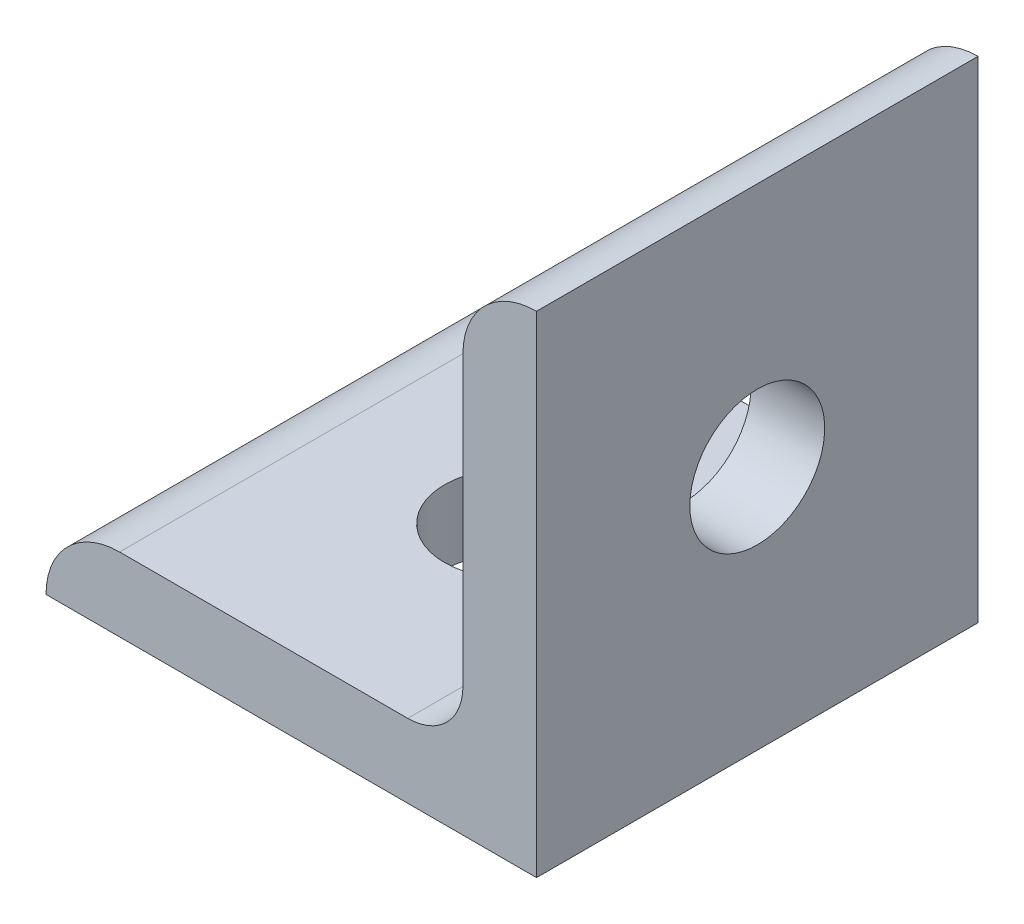
SolidWorks part; units mm, degrees
ref_plane "Front Plane" through (0, 0, 0) normal (0, 0, 1) x (1, 0, 0)
ref_plane "Top Plane" through (0, 0, 0) normal (0, 1, 0) x (1, 0, 0)
ref_plane "Right Plane" through (0, 0, 0) normal (1, 0, 0) x (0, 0, -1)
sketch "Sketch1" plane through (0, 0, 0) normal (0, 0, 1) x (1, 0, 0)
  line L0 (0, 0) -> (0, 20)
  line L1 (0, 0) -> (-20, 0)
  line L2 (-17, 3) -> (-5.25, 3)
  line L3 (-3, 5.25) -> (-3, 17)
  arc A0 (-20, 0) -> (-17, 3) centre (-17, 0) cw
  arc A1 (-3, 17) -> (0, 20) centre (0, 17) cw
  arc A2 (-5.25, 3) -> (-3, 5.25) centre (-5.25, 5.25) ccw
  point P11 (-11.125, 3)
  point P12 (-3, 11.125)
  dimension "D1" = 3
  dimension "D3" = 2.25
  dimension "D" = 3
  dimension "D2" = 3
  dimension "B" = 20
  dimension "C" = 20
extrude "Extrude1" add sketch "Sketch1" against normal mid plane 18
sketch "Sketch2" plane through (0, 3, 0) normal (0, 1, 0) x (1, 0, 0)
  circle A0 centre (-10, 0) radius 2.75
  dimension "hole" = 5.5
  dimension "hole height" = 10
extrude "Cut-Extrude1" cut sketch "Sketch2" against normal through all
sketch "Sketch3" plane through (-3, 0, 0) normal (-1, 0, 0) x (0, 0, 1)
  circle A0 centre (0, 10) radius 2.75
  dimension "D1" = 5.5
  dimension "D2" = 10
extrude "Cut-Extrude2" cut sketch "Sketch3" against normal through all
sketch "Sketch4" [suppressed] plane through (0, 6, 0) normal (0, 1, 0) x (1, 0, 0)
  line L0 (-84, 0) -> (-47.25, 0) construction
  line L1 (-47.25, 0) -> (-10.5, 0) construction
  circle A0 centre (-22.5, 0) radius 4.5
  circle A1 centre (-67.5, 0) radius 4.5
  dimension "D1" = 5.5
  dimension "D2" = 10
  dimension "D3" = 20
extrude "Cut-Extrude3" [suppressed] cut sketch "Sketch4" against normal through all
sketch "Sketch5" [suppressed] plane through (-6, 0, 0) normal (-1, 0, 0) x (0, 0, 1)
  circle A0 centre (0, 67.5) radius 4.5
  circle A1 centre (0, 22.5) radius 4.5
  dimension "D1" = 5.5
  dimension "D3" = 20
  dimension "D2" = 10
extrude "Cut-Extrude4" [suppressed] cut sketch "Sketch5" against normal through all
sketch "Sketch6" [suppressed] plane through (0, 3, 0) normal (0, 1, 0) x (1, 0, 0)
  line L0 (-10, 12.75) -> (-10, 19) construction
  line L1 (-5.25, -19) -> (-17, -19) construction
  line L2 (-10, -12.75) -> (-10, -19) construction
  line L3 (-5.25, 19) -> (-17, 19) construction
  circle A0 centre (-10, 10) radius 2.75
  circle A1 centre (-10, -10) radius 2.75
  dimension "D1" = 5.5
  dimension "D2" = 10
  dimension "distance" = 25.4
extrude "Cut-Extrude5" [suppressed] cut sketch "Sketch6" against normal through all
sketch "Sketch7" [suppressed] plane through (-3, 0, 0) normal (-1, 0, 0) x (0, 0, 1)
  line L0 (12.75, 10) -> (19, 10) construction
  line L2 (-12.75, 10) -> (-19, 10) construction
  line L4 (-19, 17) -> (-19, 5.25) construction
  line L5 (19, 17) -> (19, 5.25) construction
  circle A0 centre (-10, 10) radius 2.75
  circle A1 centre (10, 10) radius 2.75
  dimension "D2" = 5.5
  dimension "D1" = 25.4
  dimension "D3" = 10
extrude "Cut-Extrude6" [suppressed] cut sketch "Sketch7" against normal through all
sketch "Sketch8" [suppressed] plane through (0, 3, 0) normal (0, 1, 0) x (1, 0, 0)
  line L0 (-10, -10) -> (-10, -19) construction
  line L1 (-10, 10) -> (-10, 19) construction
  line L2 (-5.25, 19) -> (-37, 19) construction
  line L3 (-5.25, -19) -> (-37, -19) construction
  circle A0 centre (-30, -10) radius 2.75
  circle A1 centre (-10, -10) radius 2.75
  circle A2 centre (-10, 10) radius 2.75
  circle A3 centre (-30, 10) radius 2.75
  dimension "D1" = 5.5
  dimension "distance" = 25.4
  dimension "D2" = 10
  dimension "D3" = 20
extrude "Cut-Extrude7" [suppressed] cut sketch "Sketch8" against normal through all
sketch "Sketch9" [suppressed] plane through (-3, 0, 0) normal (-1, 0, 0) x (0, 0, 1)
  line L0 (10, 10) -> (19, 10) construction
  line L1 (-10, 10) -> (-19, 10) construction
  line L2 (-19, 37) -> (-19, 5.25) construction
  line L3 (19, 37) -> (19, 5.25) construction
  circle A0 centre (10, 10) radius 2.75
  circle A1 centre (10, 30) radius 2.75
  circle A2 centre (-10, 10) radius 2.75
  circle A3 centre (-10, 30) radius 2.75
  dimension "D1" = 5.5
  dimension "D2" = 25.4
  dimension "D3" = 10
  dimension "D4" = 20
extrude "Cut-Extrude8" [suppressed] cut sketch "Sketch9" against normal through all
equation "\"D2@Sketch1\" = \"D@Sketch1\""
equation "\"D3@Sketch1\" = \"D1@Sketch1\"*.750"
equation "\"D1@Sketch3\" = \"hole@Sketch2\""
equation "\"D1@Sketch4\" = \"hole@Sketch2\""
equation "\"D1@Sketch5\" = \"hole@Sketch2\""
equation "\"D1@Sketch6\" = \"hole@Sketch2\""
equation "\"D2@Sketch7\" = \"hole@Sketch2\""
equation "\"D1@Sketch7\" = \"distance@Sketch6\""
equation "\"D1@Sketch8\" = \"hole@Sketch2\""
equation "\"D1@Sketch9\" = \"hole@Sketch2\""
equation "\"D2@Sketch9\" = \"distance@Sketch8\""
equation "\"D2@Sketch3\" = \"hole height@Sketch2\""
equation "\"D2@Sketch6\" = \"hole height@Sketch2\""
equation "\"D3@Sketch7\" = \"hole height@Sketch2\""
equation "\"D2@Sketch4\" = \"hole height@Sketch2\""
equation "\"D3@Sketch4\" = \"hole height@Sketch2\"*2"
equation "\"D2@Sketch5\" = \"hole height@Sketch2\""
equation "\"D3@Sketch5\" = \"hole height@Sketch2\"*2"
equation "\"D2@Sketch8\" = \"hole height@Sketch2\""
equation "\"D3@Sketch8\" = \"hole height@Sketch2\"*2"
equation "\"D3@Sketch9\" = \"hole height@Sketch2\""
equation "\"D4@Sketch9\" = \"hole height@Sketch2\"*2"
